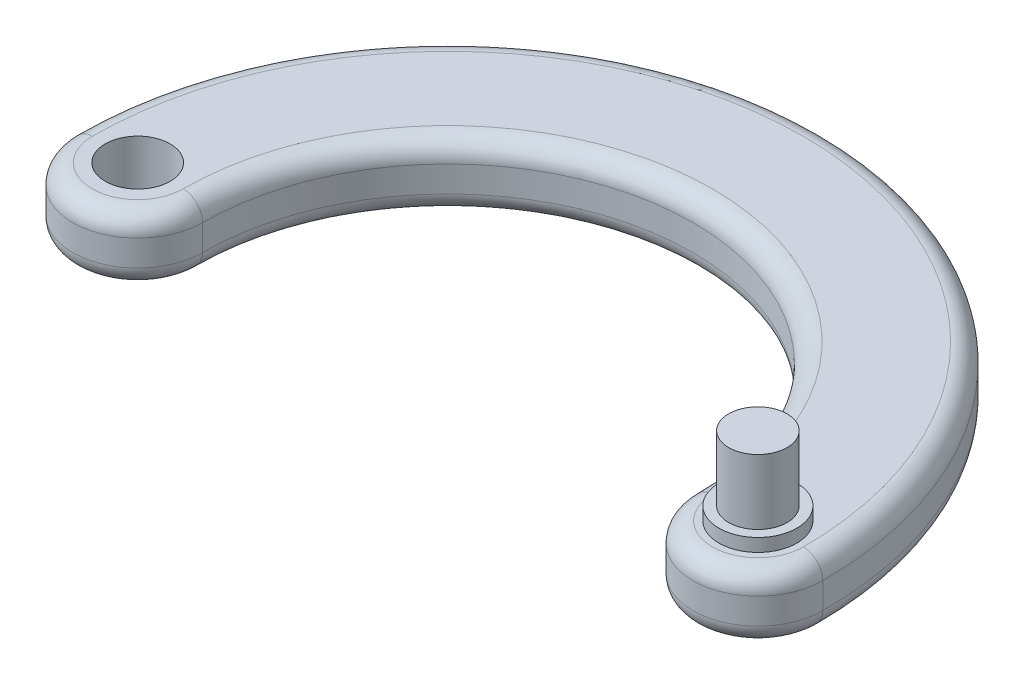
SolidWorks part; units mm, degrees
ref_plane "Front Plane" through (0, 0, 0) normal (0, 0, 1) x (1, 0, 0)
ref_plane "Top Plane" through (0, 0, 0) normal (0, 1, 0) x (1, 0, 0)
ref_plane "Right Plane" through (0, 0, 0) normal (1, 0, 0) x (0, 0, -1)
sketch "Sketch1" plane through (0, 0, 0) normal (0, 1, 0) x (1, 0, 0)
  circle A0 centre (-95.5, 0) radius 5
  circle A1 centre (0, 0) radius 5
  arc A2 (-10, 0) -> (10, 0) centre (0, 0) ccw
  arc A3 (-105.5, 0) -> (-85.5, 0) centre (-95.5, 0) ccw
  arc A4 (-10, 0) -> (-85.5, 0) centre (-47.75, 0) ccw
  arc A5 (10, 0) -> (-105.5, 0) centre (-47.75, 0) ccw
  circle A6 centre (-95.5, 0) radius 10 construction
  circle A7 centre (0, 0) radius 10 construction
  dimension "D1" = 5
extrude "Boss-Extrude1" add sketch "Sketch1" along normal blind 10
sketch "Sketch2" plane through (0, 10, 0) normal (0, 1, 0) x (1, 0, 0)
  circle A0 centre (0, 0) radius 4.5
extrude "Boss-Extrude2" add sketch "Sketch2" along normal blind 12 and the other way up to surface (10 mm away) other way up to face at (-47.75, 0, -18.875)
sketch "Sketch3" plane through (0, 10, 0) normal (0, 1, 0) x (1, 0, 0)
  circle A0 centre (0, 0) radius 5
extrude "Boss-Extrude3" add sketch "Sketch3" against normal up to surface (10 mm away) up to face at (-47.75, 0, -18.875)
sketch "Sketch4" plane through (0, 10, 0) normal (0, 1, 0) x (1, 0, 0)
  circle A0 centre (0, 0) radius 6
extrude "Boss-Extrude4" add sketch "Sketch4" along normal blind 2
fillet "Fillet1" radius 3 8 edges at (0, 0, 10) (-47.75, 0, -37.75) (-95.5, 0, 10) (-47.75, 0, -57.75) (0, 10, 10) (-95.5, 10, 10) (-47.75, 10, -57.75) (-47.75, 10, -37.75)
